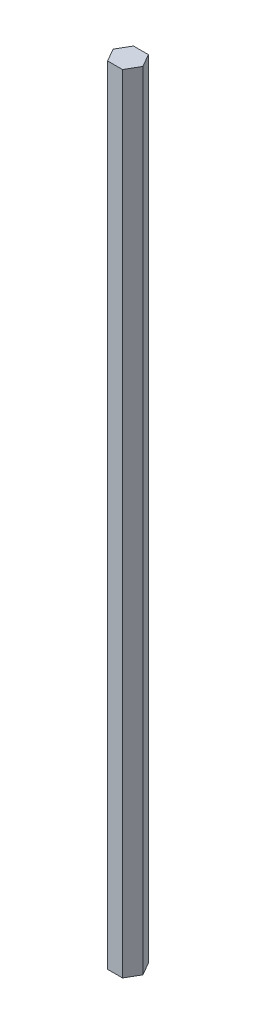
SolidWorks part; units mm, degrees
ref_plane "Front Plane" through (0, 0, 0) normal (0, 0, 1) x (1, 0, 0)
ref_plane "Top Plane" through (0, 0, 0) normal (0, 1, 0) x (1, 0, 0)
ref_plane "Right Plane" through (0, 0, 0) normal (1, 0, 0) x (0, 0, -1)
sketch "Sketch1" plane through (0, 0, 0) normal (0, 1, 0) x (1, 0, 0)
  line L1 (0.1203, -2.3865) -> (3.4934, 3.4559)
  line L2 (3.4934, 3.4559) -> (0.1203, 9.2984)
  line L3 (0.1203, 9.2984) -> (-6.626, 9.2984)
  line L4 (-6.626, 9.2984) -> (-9.9991, 3.4559)
  line L5 (-9.9991, 3.4559) -> (-6.626, -2.3865)
  line L6 (-6.626, -2.3865) -> (0.1203, -2.3865)
  circle A0 centre (-3.2529, 3.4559) radius 5.8424 construction
  dimension "D1" = 6.7462
  dimension "D2" = 6.7462
extrude "Boss-Extrude1" add sketch "Sketch1" along normal blind 355.6
